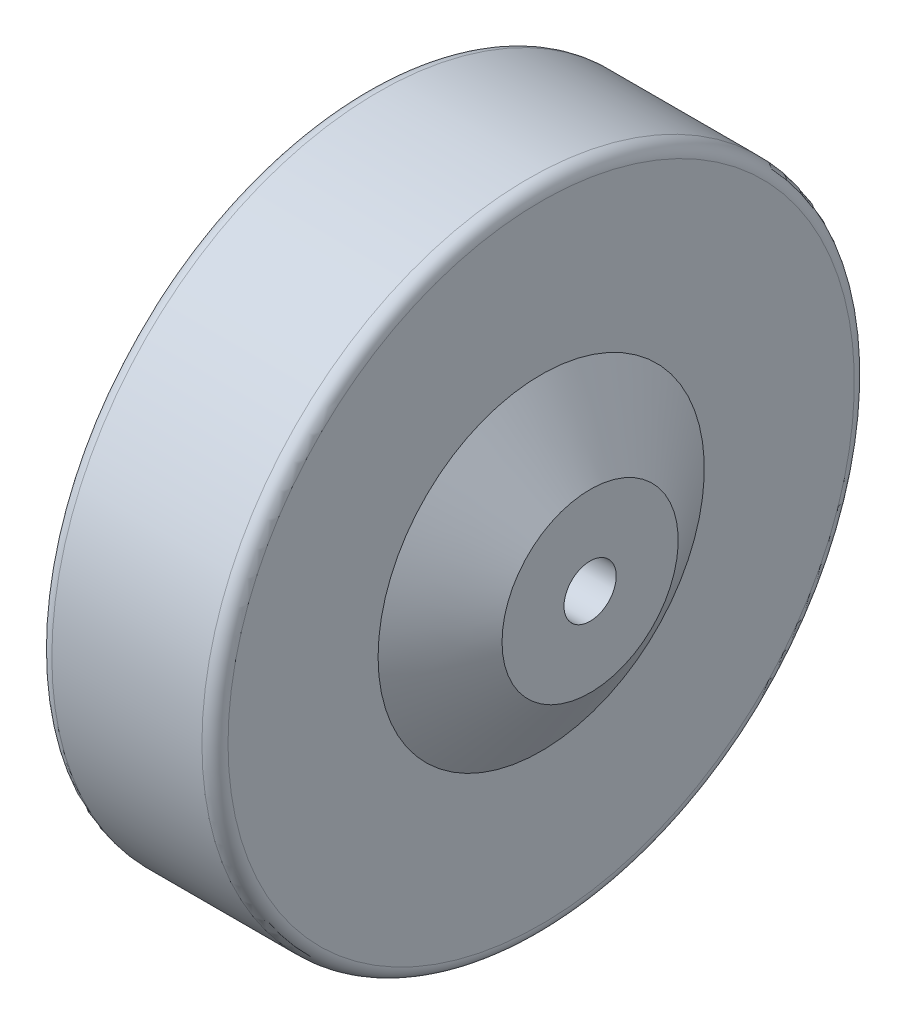
SolidWorks part; units mm, degrees
material "AISI 1020"
ref_plane "Спереди" through (0, 0, 0) normal (0, 0, 1) x (1, 0, 0)
ref_plane "Сверху" through (0, 0, 0) normal (0, 1, 0) x (1, 0, 0)
ref_plane "Справа" through (0, 0, 0) normal (1, 0, 0) x (0, 0, -1)
sketch "Эскиз1" plane through (0, 0, 0) normal (0, 0, 1) x (1, 0, 0)
  line L0 (-557.6633, 0) -> (27325.4994, 0) construction
  line L1 (0, -557.6633) -> (0, 27325.4994) construction
  line L2 (21, 4) -> (-21, 4)
  line L3 (-21, 4) -> (-21, 13.5)
  line L4 (-21, 13.5) -> (-13.5, 25)
  line L5 (-13.5, 25) -> (-13.5, 48)
  line L6 (-11.5, 50) -> (11.5, 50)
  line L7 (21, 4) -> (21, 13.5)
  line L8 (21, 13.5) -> (13.5, 25)
  line L9 (13.5, 25) -> (13.5, 48)
  arc A0 (-13.5, 48) -> (-11.5, 50) centre (-11.5, 48) cw
  arc A1 (13.5, 48) -> (11.5, 50) centre (11.5, 48) ccw
  point P14 (0, 4)
  point P19 (0, 50)
  dimension "D7" = 2
  dimension "D1" = 100
  dimension "D2" = 27
  dimension "D3" = 42
  dimension "D4" = 8
  dimension "D5" = 50
  dimension "D6" = 27
revolve "Повернуть1" add sketch "Эскиз1" angle 360 about L0
